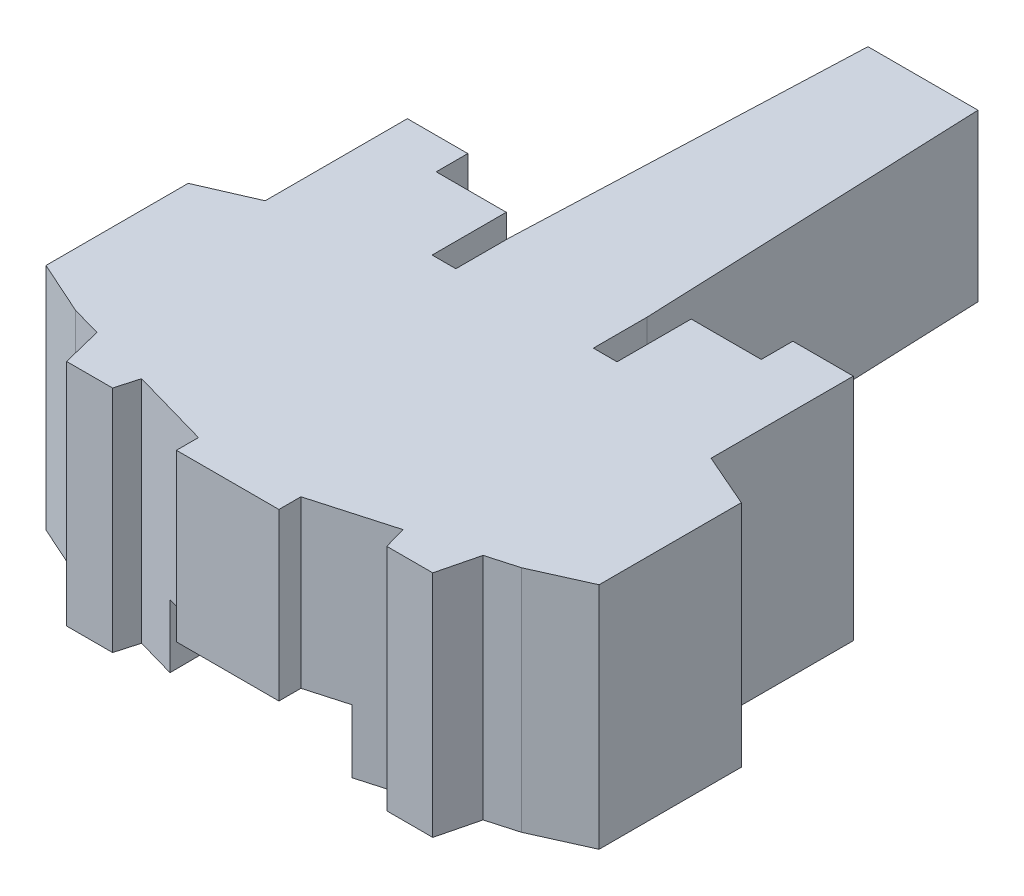
SolidWorks part; units mm, degrees
ref_plane "Front Plane" through (0, 0, 0) normal (0, 0, 1) x (1, 0, 0)
ref_plane "Top Plane" through (0, 0, 0) normal (0, 1, 0) x (1, 0, 0)
ref_plane "Right Plane" through (0, 0, 0) normal (1, 0, 0) x (0, 0, -1)
sketch "Sketch1" plane through (0, 0, 0) normal (0, 1, 0) x (1, 0, 0)
  line L0 (189.3756, 496.5449) -> (821.9605, 485.5031) construction
  line L1 (66.1046, 65.3579) -> (66.1046, 21.3579) construction
  line L2 (69.5865, 65.3579) -> (62.6228, 65.3579)
  line L3 (69.5865, 65.3579) -> (70.4558, 43.5381)
  line L4 (70.4558, 43.5381) -> (70.4558, 40.1478)
  line L5 (70.4558, 40.1478) -> (71.9558, 40.1478)
  line L6 (71.9558, 40.1478) -> (71.9558, 44.8392)
  line L7 (71.9558, 44.8392) -> (76.3893, 44.8392)
  line L8 (76.3893, 44.8392) -> (76.3893, 46.8392)
  line L9 (76.3893, 46.8392) -> (80.2143, 46.8392)
  line L10 (80.2143, 46.8392) -> (80.2143, 37.8392)
  line L11 (80.2143, 37.8392) -> (83.6046, 36.3613)
  line L12 (83.6046, 36.3613) -> (83.6046, 27.3613)
  line L13 (83.6046, 27.3613) -> (80.2143, 25.8392)
  line L14 (80.2143, 25.8392) -> (78.3232, 25.3017)
  line L15 (69.3478, 22.751) -> (69.3478, 21.3579)
  line L16 (69.3478, 21.3579) -> (62.8614, 21.3579)
  line L17 (62.8614, 22.751) -> (62.8614, 21.3579)
  line L18 (51.9949, 25.8392) -> (53.8861, 25.3017)
  line L19 (48.6046, 27.3613) -> (51.9949, 25.8392)
  line L20 (48.6046, 36.3613) -> (48.6046, 27.3613)
  line L21 (51.9949, 37.8392) -> (48.6046, 36.3613)
  line L22 (51.9949, 46.8392) -> (51.9949, 37.8392)
  line L23 (55.8199, 46.8392) -> (51.9949, 46.8392)
  line L24 (55.8199, 44.8392) -> (55.8199, 46.8392)
  line L25 (60.2534, 44.8392) -> (55.8199, 44.8392)
  line L26 (60.2534, 40.1478) -> (60.2534, 44.8392)
  line L27 (61.7534, 40.1478) -> (60.2534, 40.1478)
  line L28 (61.7534, 43.5381) -> (61.7534, 40.1478)
  line L29 (62.6228, 65.3579) -> (61.7534, 43.5381)
  line L30 (78.3232, 25.3017) -> (77.6888, 22.751)
  line L31 (77.6888, 22.751) -> (74.7811, 22.751)
  line L32 (74.7811, 22.751) -> (74.375, 24.1797)
  line L33 (74.375, 24.1797) -> (69.3478, 22.751)
  line L34 (53.8861, 25.3017) -> (54.5204, 22.751)
  line L35 (54.5204, 22.751) -> (57.4282, 22.751)
  line L36 (57.4282, 22.751) -> (57.8342, 24.1797)
  line L37 (57.8342, 24.1797) -> (62.8614, 22.751)
  dimension "D1" = 17.5
  dimension "D2" = 12
  dimension "D3" = 3.0881
  dimension "D4" = 1.4778
  dimension "D5" = 9
  dimension "D6" = 2
  dimension "D7" = 1.5
  dimension "D8" = 14.2568
  dimension "D9" = 3.825
  dimension "D10" = 4.4335
  dimension "D11" = 3.4819
  dimension "D12" = 44
  dimension "D13" = 9
  dimension "D14" = 48.6046
  dimension "D15" = 51.9949
  dimension "D16" = 53.8861
  dimension "D17" = 54.5204
  dimension "D18" = 57.4282
  dimension "D19" = 21.3579
  dimension "D20" = 22.751
  dimension "D23" = 40.1478
  dimension "D24" = 43.5381
extrude "Boss-Extrude1" add sketch "Sketch1" along normal blind 14.5
sketch "Sketch2" plane through (0, 0, 0) normal (0, -1, 0) x (-1, 0, 0)
  line L0 (-66.1046, 21.3579) -> (-66.1046, 65.3579) construction
  line L1 (-62.8614, 21.3579) -> (-69.3478, 21.3579) construction
  line L2 (-69.5865, 65.3579) -> (-62.6228, 65.3579) construction
  line L3 (-60.2534, 40.1478) -> (-60.3478, 23.4654)
  line L4 (-57.8342, 24.1797) -> (-62.8614, 22.751) construction
  line L5 (-60.3478, 23.4654) -> (-62.8614, 22.751)
  line L6 (-62.8614, 22.751) -> (-62.8614, 21.3579)
  line L7 (-62.8614, 21.3579) -> (-69.3478, 21.3579)
  line L8 (-69.3478, 21.3579) -> (-69.3478, 22.751)
  line L9 (-69.3478, 22.751) -> (-71.8614, 23.4654)
  line L10 (-69.3478, 22.751) -> (-74.375, 24.1797) construction
  line L11 (-71.8614, 23.4654) -> (-71.9558, 40.1478)
  line L12 (-71.9558, 40.1478) -> (-70.4558, 40.1478)
  line L13 (-70.4558, 40.1478) -> (-70.4558, 43.5381)
  line L14 (-70.4558, 43.5381) -> (-69.5865, 65.3579)
  line L15 (-69.5865, 65.3579) -> (-62.6228, 65.3579)
  line L16 (-62.6228, 65.3579) -> (-61.7534, 43.5381)
  line L17 (-61.7534, 43.5381) -> (-61.7534, 40.1478)
  line L18 (-61.7534, 40.1478) -> (-60.2534, 40.1478)
  line L19 (-48.6046, 36.3613) -> (-48.6046, 27.3613) construction
  circle A0 centre (-66.1046, 40.8079) radius 2.5
  dimension "D1" = 5
  dimension "D2" = 13.6103
  dimension "D3" = 18.0569
extrude "Cut-Extrude1" cut sketch "Sketch2" against normal blind 4
